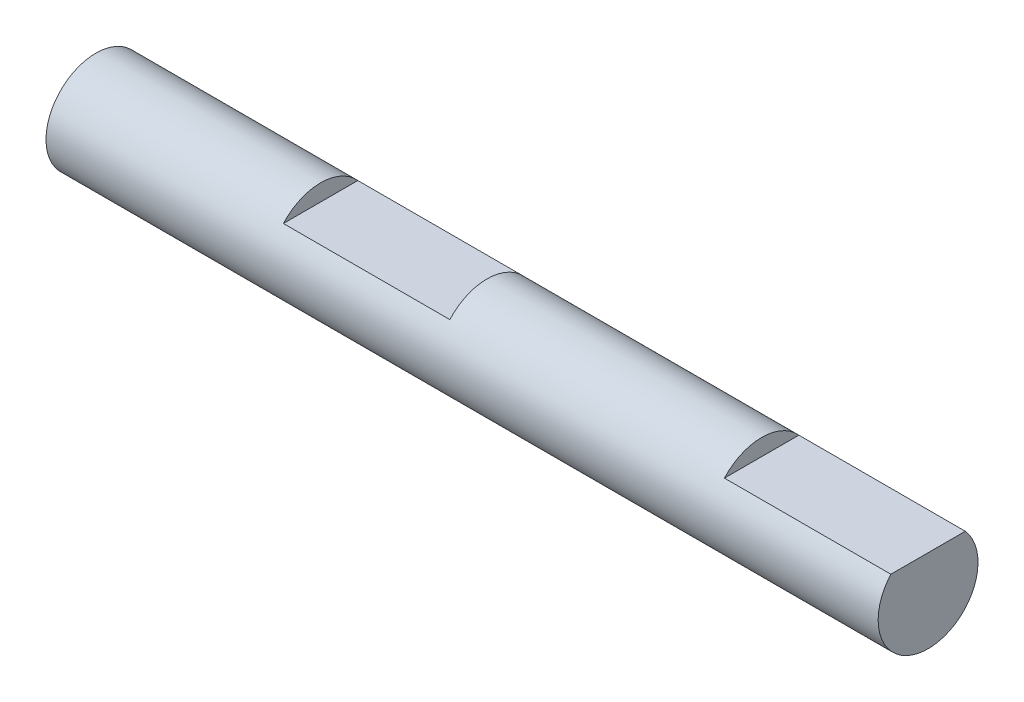
SolidWorks part; units mm, degrees
material "1.0037 (S235JR)"
ref_plane "Vorne" through (0, 0, 0) normal (0, 0, 1) x (1, 0, 0)
ref_plane "Oben" through (0, 0, 0) normal (0, 1, 0) x (1, 0, 0)
ref_plane "Rechts" through (0, 0, 0) normal (1, 0, 0) x (0, 0, -1)
sketch "Skizze1" plane through (0, 0, 0) normal (0, 0, 1) x (1, 0, 0)
  line L0 (0, 0) -> (61.515, 0) construction
  line L2 (0, 0) -> (50, 0)
  line L3 (0, 0) -> (0, 3)
  line L4 (0, 3) -> (50, 3)
  line L5 (50, 0) -> (50, 3)
  dimension "D1" = 50
  dimension "D2" = 6
revolve "Rotation1" add sketch "Skizze1" angle 360 about L0
sketch "Skizze2" plane through (0, 0, 0) normal (0, 0, 1) x (1, 0, 0)
  line L0 (50, -3) -> (50, 3) construction
  line L1 (13.5, 4) -> (23.5, 4)
  line L2 (13.5, 4) -> (13.5, 2)
  line L3 (13.5, 2) -> (23.5, 2)
  line L4 (23.5, 4) -> (23.5, 2)
  line L5 (40, 4) -> (50, 4)
  line L6 (40, 4) -> (40, 2)
  line L7 (40, 2) -> (50, 2)
  line L8 (50, 4) -> (50, 2)
  line L9 (0, -3) -> (50, -3) construction
  dimension "D1" = 2
  dimension "D2" = 13.5
  dimension "D3" = 10
  dimension "D4" = 2
  dimension "D5" = 5
  dimension "D6" = 10
  dimension "D7" = 2
extrude "Schnitt-Linear austragen1" cut sketch "Skizze2" against normal through all and the other way through all
move or copy body "Körper-Verschieben/Kopieren1" [suppressed] bodies to move or copy 104
